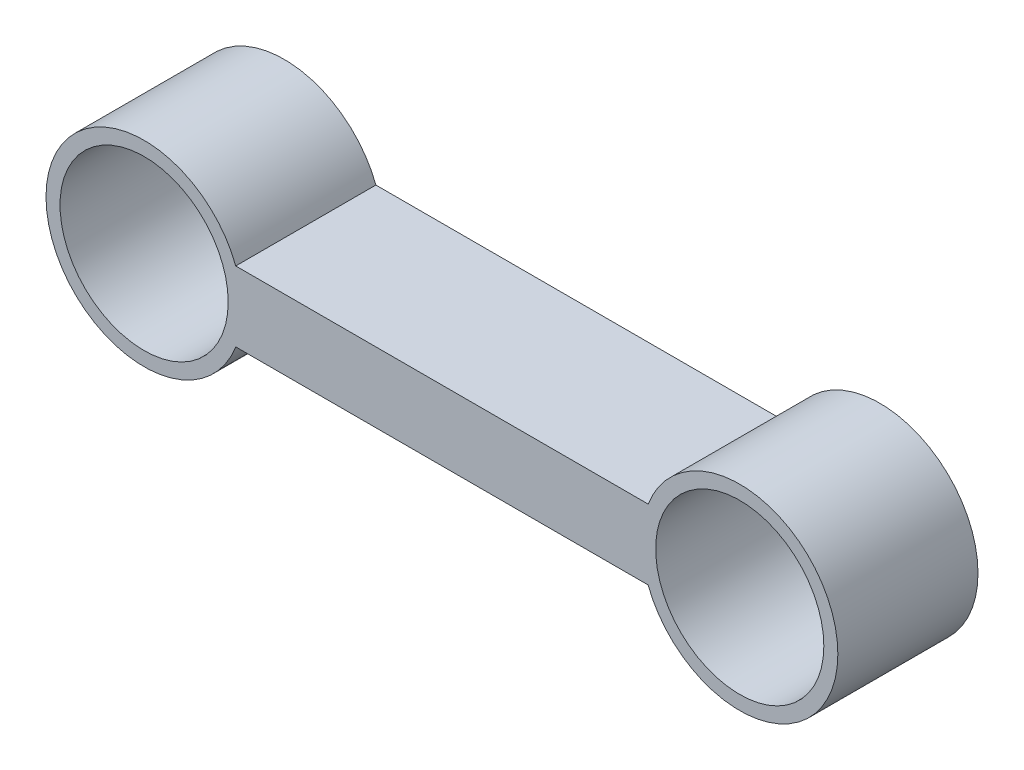
SolidWorks part; units mm, degrees
ref_plane "Front Plane" through (0, 0, 0) normal (0, 0, 1) x (1, 0, 0)
ref_plane "Top Plane" through (0, 0, 0) normal (0, 1, 0) x (1, 0, 0)
ref_plane "Right Plane" through (0, 0, 0) normal (1, 0, 0) x (0, 0, -1)
sketch "Sketch1" plane through (0, 0, 0) normal (0, 0, 1) x (1, 0, 0)
  line L1 (91.3426, -6.35) -> (16.6074, -6.35)
  line L2 (91.3426, -6.35) -> (91.3426, 6.35)
  line L3 (91.3426, 6.35) -> (16.6074, 6.35)
  line L4 (16.6074, -6.35) -> (16.6074, 6.35)
  line L5 (91.3426, -6.35) -> (16.6074, 6.35) construction
  line L6 (91.3426, 6.35) -> (16.6074, -6.35) construction
  circle A0 centre (0, 0) radius 15.24
  circle A1 centre (107.95, 0) radius 15.24
  circle A2 centre (0, 0) radius 17.78
  circle A3 centre (107.95, 0) radius 17.78
  point P5 (53.975, 0)
  point P14 (90.8554, 4.8892)
  point P15 (0, 0)
  point P16 (0, 0)
  dimension "D1" = 30.48
  dimension "D2" = 107.95
  dimension "D4" = 12.7
  dimension "D3" = 2.54
extrude "Boss-Extrude1" add sketch "Sketch1" along normal blind 25.4 contours L4 A2 A0 | A3 L3 A2 L1 | L4 A2 | L2 A3 A1 | L2 A3
